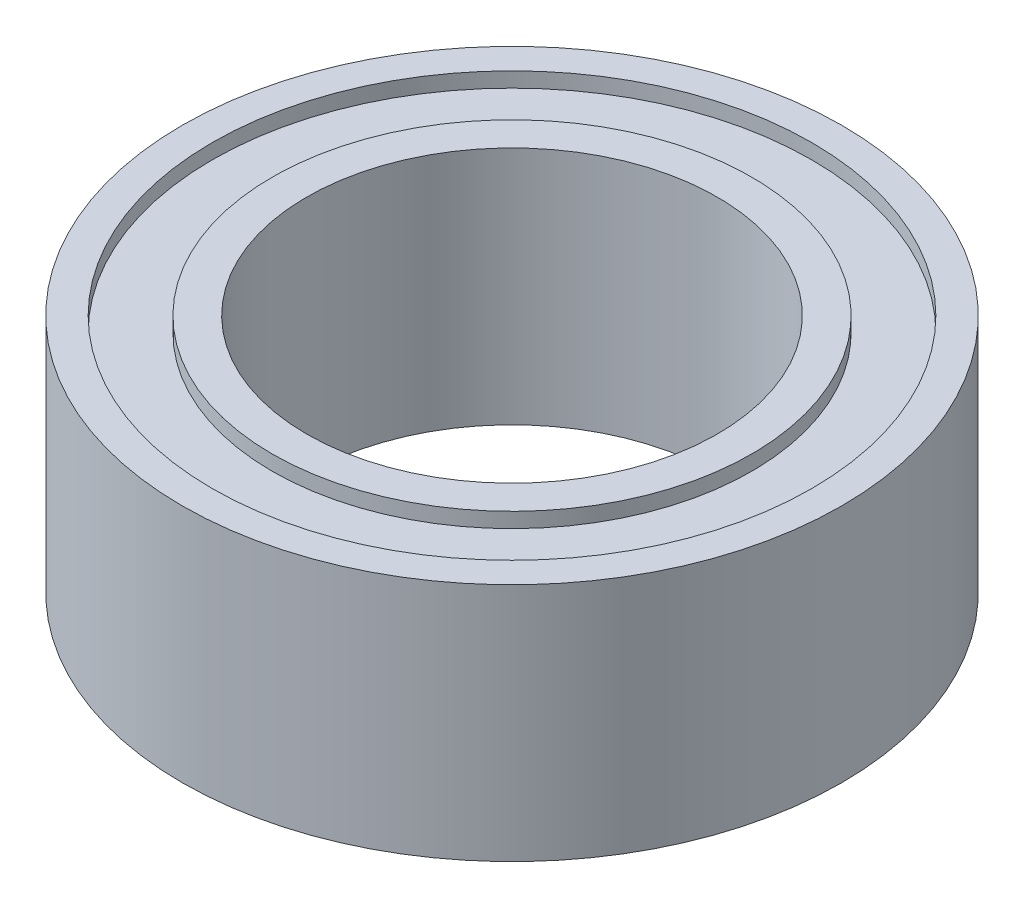
SolidWorks part; units mm, degrees
ref_plane "Front Plane" through (0, 0, 0) normal (0, 0, 1) x (1, 0, 0)
ref_plane "Top Plane" through (0, 0, 0) normal (0, 1, 0) x (1, 0, 0)
ref_plane "Right Plane" through (0, 0, 0) normal (1, 0, 0) x (0, 0, -1)
sketch "Sketch1" plane through (0, 0, 0) normal (0, 1, 0) x (1, 0, 0)
  circle A0 centre (0, 0) radius 11
  dimension "D1" = 22
extrude "Boss-Extrude1" add sketch "Sketch1" along normal mid plane 8
sketch "Sketch2" plane through (0, 4, 0) normal (0, 1, 0) x (1, 0, 0)
  circle A0 centre (0, 0) radius 6.85
  dimension "19.9" = 13.7
extrude "Cut-Extrude1" cut sketch "Sketch2" against normal blind 11.96
sketch "Sketch3" plane through (0, 4, 0) normal (0, 1, 0) x (1, 0, 0)
  circle A0 centre (0, 0) radius 9 construction
  circle A1 centre (0, 0) radius 10
  circle A2 centre (0, 0) radius 8
  dimension "D1" = 18
  dimension "D2" = 1
  dimension "D3" = 1
extrude "Cut-Extrude2" cut sketch "Sketch3" against normal blind 0.5
mirror "Mirror1" about plane through (0, 0, 0) normal (0, 1, 0) of "Cut-Extrude2"
